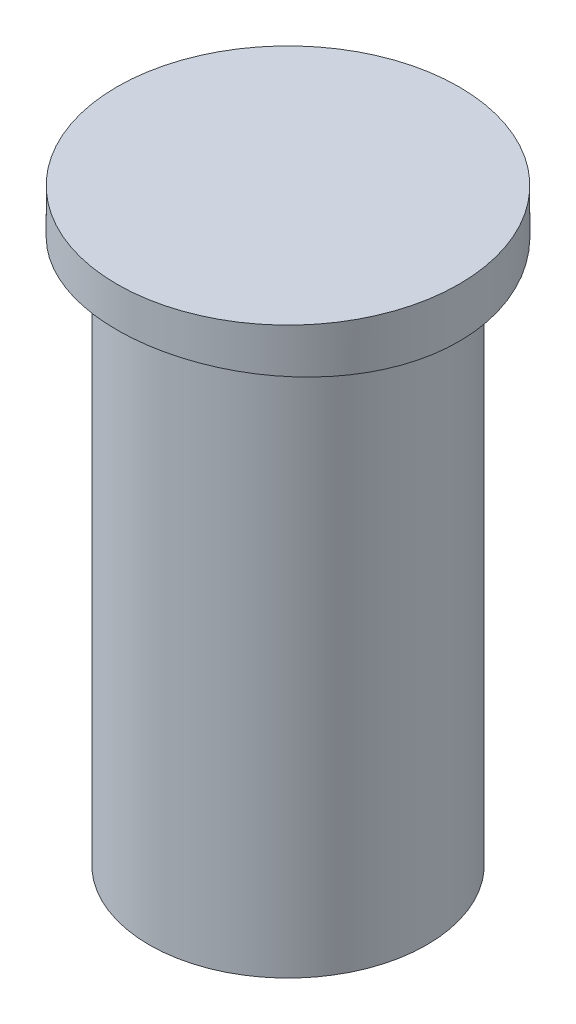
SolidWorks part; units mm, degrees
ref_plane "Front Plane" through (0, 0, 0) normal (0, 0, 1) x (1, 0, 0)
ref_plane "Top Plane" through (0, 0, 0) normal (0, 1, 0) x (1, 0, 0)
ref_plane "Right Plane" through (0, 0, 0) normal (1, 0, 0) x (0, 0, -1)
sketch "Sketch1" plane through (0, 0, 0) normal (0, 1, 0) x (1, 0, 0)
  circle A0 centre (0, 0) radius 6.1849
extrude "Boss-Extrude1" add sketch "Sketch1" along normal blind 23.9776
sketch "Sketch2" plane through (0, 23.9776, 0) normal (0, 1, 0) x (1, 0, 0)
  circle A0 centre (0, 0) radius 7.62
extrude "Boss-Extrude2" add sketch "Sketch2" along normal blind 2.2352
sketch "Sketch4" plane through (0, 23.9776, 0) normal (0, -1, 0) x (1, 0, 0)
  circle A0 centre (0, 0) radius 7.62
  circle A1 centre (0, 0) radius 6.1849
extrude "Cut-Extrude2" cut sketch "Sketch4" against normal blind 0.0254 and the other way through all
sketch "Sketch8" plane through (0, 0, 0) normal (0, 0, 1) x (1, 0, 0)
  line L0 (-7.62, 24.003) -> (7.62, 24.003)
  arc A1 (-7.62, 24.003) -> (7.62, 24.003) centre (0, -40.9566) cw
extrude "Cut-Extrude3" cut sketch "Sketch8" against normal through all both and the other way through all
